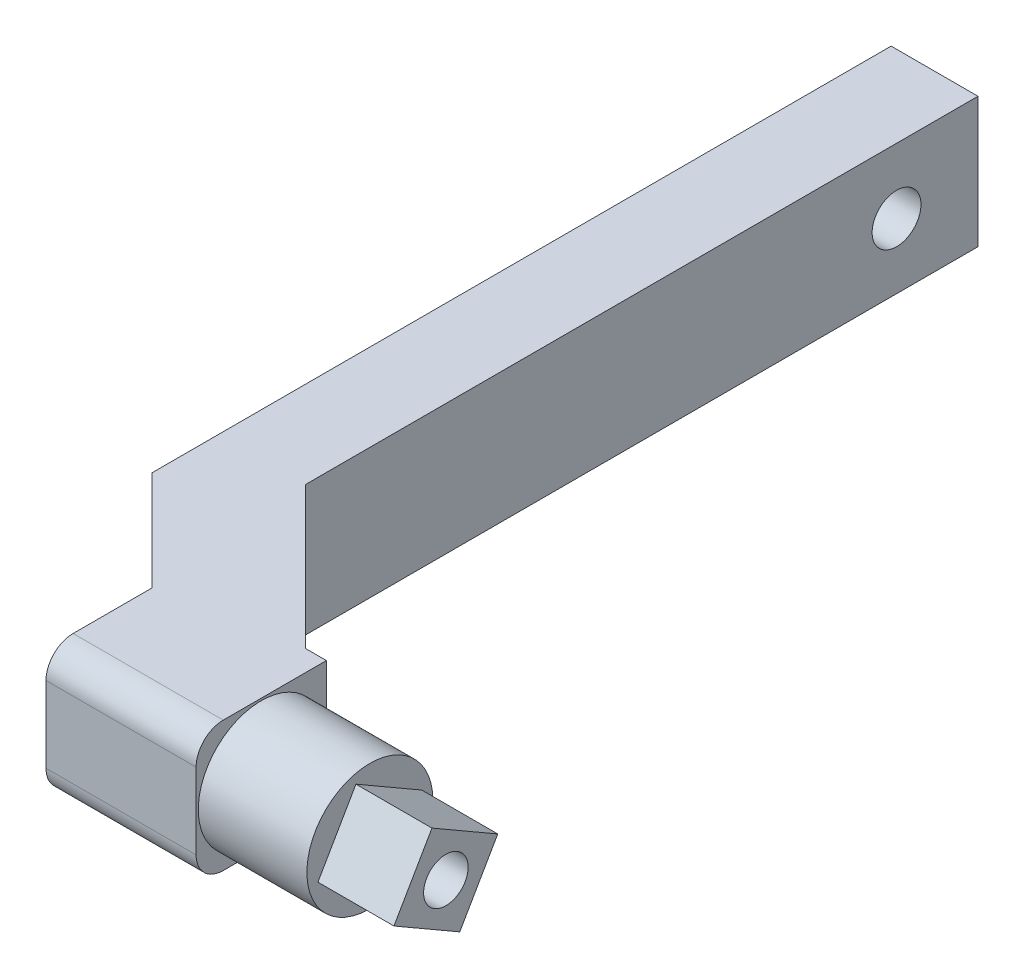
SolidWorks part; units mm, degrees
ref_plane "Front Plane" through (0, 0, 0) normal (0, 0, 1) x (1, 0, 0)
ref_plane "Top Plane" through (0, 0, 0) normal (0, 1, 0) x (1, 0, 0)
ref_plane "Right Plane" through (0, 0, 0) normal (1, 0, 0) x (0, 0, -1)
sketch "Эскиз1" plane through (0, 0, 0) normal (0, 1, 0) x (1, 0, 0)
  line L0 (0, 0) -> (-14.1421, -14.1421)
  line L1 (0, 0) -> (-37.8579, 37.8579)
  line L2 (-14.1421, -14.1421) -> (-52, 23.7157)
  line L3 (-37.8579, 37.8579) -> (-52, 23.7157)
  line L4 (-33.6421, 5.3579) -> (-33.6421, -14.1421)
  line L5 (-14.1421, -14.1421) -> (14, -14.1421)
  line L6 (-14.1421, -14.1421) -> (-14.1421, 9.8579)
  line L7 (-14.1421, 9.8579) -> (14, 9.8579)
  line L8 (14, -14.1421) -> (14, 9.8579)
  line L9 (-52, 23.7157) -> (-36, 23.7157)
  line L10 (-52, 23.7157) -> (-52, 159.8579)
  line L11 (-52, 159.8579) -> (-36, 159.8579)
  line L12 (-36, 23.7157) -> (-36, 159.8579)
  line L13 (-33.6421, -14.1421) -> (-14.1421, -14.1421)
  point P13 (14, -2.1421)
  dimension "D1" = 20
  dimension "D2" = 24
  dimension "D3" = 14
  dimension "D4" = 50
  dimension "D5" = 16
  dimension "D6" = 150
  dimension "D7" = 45
  dimension "D8" = 7.5
extrude "Бобышка-Вытянуть1" add sketch "Эскиз1" along normal blind 24 contours L1 L12 L11 L10 L3 | L9 L12 L1 L3 | L12 L9 L2 L6 L7 L1 | L7 L6 L0 L1 | L5 L8 L7 L1 L0 | L4 L13 L2
sketch "Эскиз2" plane through (14, 0, 0) normal (1, 0, 0) x (0, 0, -1)
  line L0 (-14.1421, 0) -> (9.8579, 24) construction
  circle A1 centre (-2.1421, 12) radius 11.6
  point P3 (-2.1421, 12)
  line M2 (-14.1421, 0) -> (9.8579, 0)
  line M3 (9.8579, 0) -> (9.8579, 24)
  line M4 (9.8579, 24) -> (-14.1421, 24)
  line M5 (-14.1421, 24) -> (-14.1421, 0)
  dimension "D1" = 23.2
extrude "Вырез-Вытянуть1" cut sketch "Эскиз2" against normal blind 20 contours A1 M5 M2 M3 M4 | L0 A1 M2 M3
sketch "Эскиз6" plane through (14, 0, 0) normal (1, 0, 0) x (0, 0, -1)
  circle A0 centre (-2.1421, 12) radius 4.1
extrude "Вырез-Вытянуть3" cut sketch "Эскиз6" against normal through all both and the other way through all
fillet "Скругление3" radius 5 2 edges at (-19.8211, 24, 14.1421) (-19.8211, 0, 14.1421)
sketch "Эскиз9" plane through (14, 0, 0) normal (1, 0, 0) x (0, 0, -1)
  line L0 (-4.7043, 21.5622) -> (-11.7043, 9.4378)
  line L1 (-4.7043, 21.5622) -> (7.42, 14.5622)
  line L2 (-11.7043, 9.4378) -> (0.42, 2.4378)
  line L3 (7.42, 14.5622) -> (0.42, 2.4378)
  line L4 (-2.1421, 23.6) -> (-2.1421, 0.4) construction
  line L5 (-2.1421, 12) -> (-12.188, 17.8) construction
  line L6 (7.42, 14.5622) -> (-11.7043, 9.4378) construction
  circle A1 centre (-2.1421, 12) radius 11.6 construction
  dimension "D1" = 14
  dimension "D2" = 14
  dimension "D3" = 60
extrude "Бобышка-Вытянуть2" add sketch "Эскиз9" along normal blind 14
sketch "Эскиз10" plane through (28, 0, 0) normal (1, 0, 0) x (0, 0, -1)
  circle A0 centre (-2.1421, 12) radius 4.1
  dimension "D1" = 8.2
extrude "Вырез-Вытянуть4" cut sketch "Эскиз10" against normal through all
sketch "Эскиз12" plane through (-52, 0, 0) normal (-1, 0, 0) x (0, 0, 1)
  line L0 (-159.8579, 24) -> (-159.8579, 0) construction
  line L1 (-144.8579, 0) -> (-144.8579, 24) construction
  line L2 (-23.7157, 0) -> (-159.8579, 0) construction
  line L3 (-23.7157, 24) -> (-159.8579, 24) construction
  circle A0 centre (-144.8579, 12) radius 11.1
  dimension "D1" = 15
extrude "Вырез-Вытянуть5" cut sketch "Эскиз12" against normal blind 7.1
sketch "Эскиз13" plane through (-44.9, 0, 0) normal (-1, 0, 0) x (0, 0, 1)
  circle A0 centre (-144.8579, 12) radius 4.5
extrude "Вырез-Вытянуть6" cut sketch "Эскиз13" against normal through all
